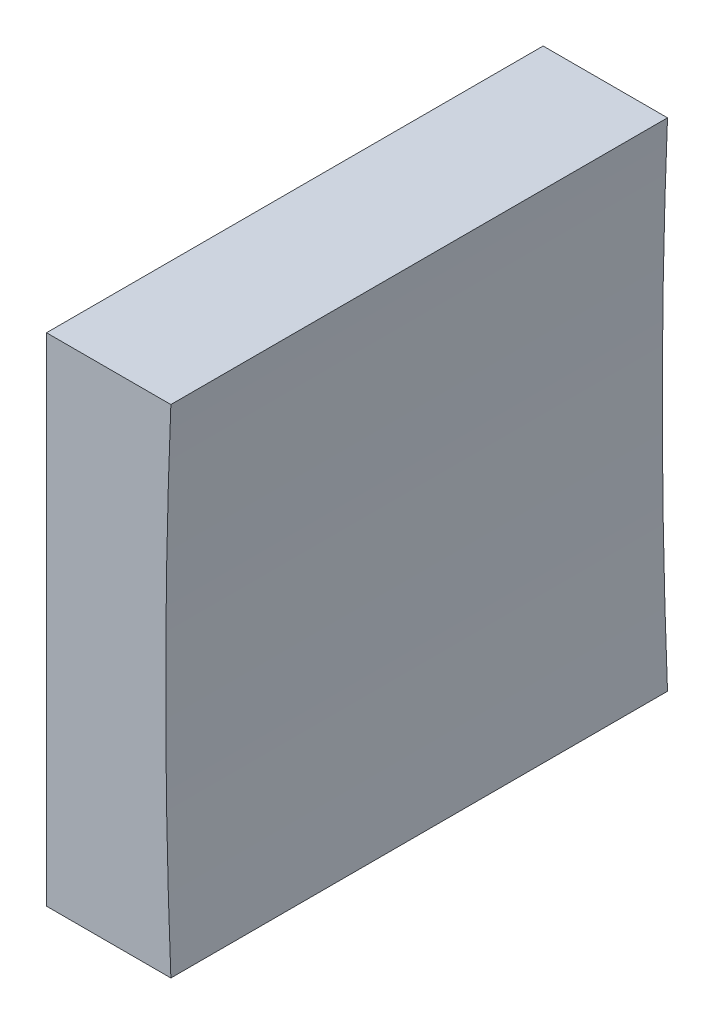
SolidWorks part; units mm, degrees
ref_plane "前视基准面" through (0, 0, 0) normal (0, 0, 1) x (1, 0, 0)
ref_plane "上视基准面" through (0, 0, 0) normal (0, 1, 0) x (1, 0, 0)
ref_plane "右视基准面" through (0, 0, 0) normal (1, 0, 0) x (0, 0, -1)
sketch "草图1" plane through (0, 0, 0) normal (0, 0, 1) x (1, 0, 0)
  line L0 (278.655, 66.8579) -> (298.183, 66.8579) construction
  line L1 (284.7071, 66.8579) -> (284.7071, 79.3579)
  line L2 (284.7071, 79.3579) -> (290.9677, 79.3579)
  line L3 (290.9677, 54.3579) -> (284.7071, 54.3579)
  line L4 (284.7071, 54.3579) -> (284.7071, 66.8579)
  arc A0 (290.9677, 79.3579) -> (290.9677, 54.3579) centre (590.7071, 66.8579) ccw
  dimension "D1" = 300
extrude "凸台-拉伸1" add sketch "草图1" along normal blind 25
